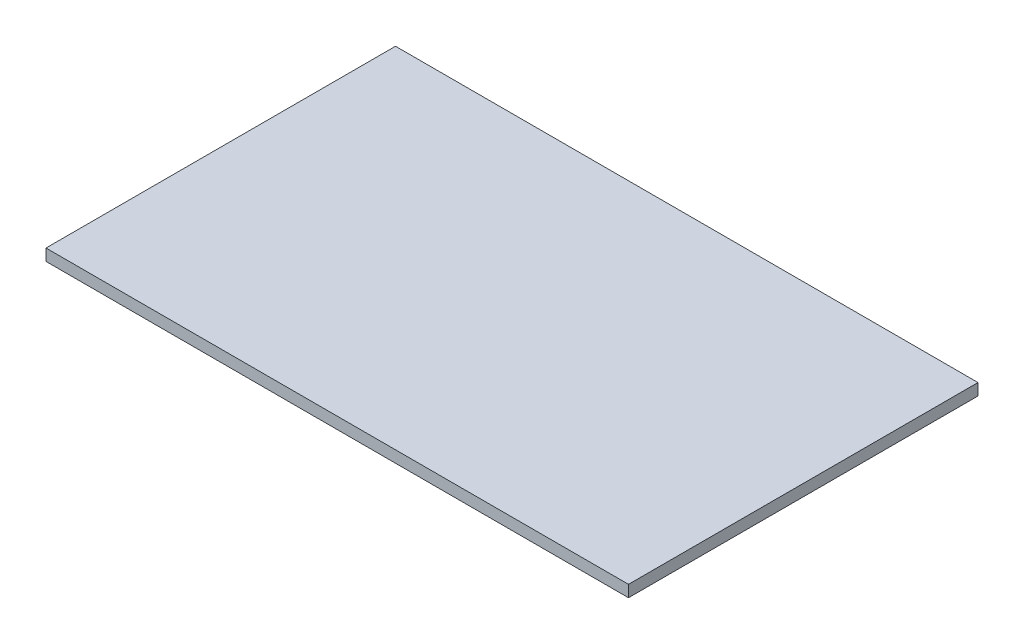
SolidWorks part; units mm, degrees
ref_plane "Front Plane" through (0, 0, 0) normal (0, 0, 1) x (1, 0, 0)
ref_plane "Top Plane" through (0, 0, 0) normal (0, 1, 0) x (1, 0, 0)
ref_plane "Right Plane" through (0, 0, 0) normal (1, 0, 0) x (0, 0, -1)
sketch "Sketch1" plane through (0, 0, 0) normal (0, 1, 0) x (1, 0, 0)
  line L1 (0, 0) -> (250, 0)
  line L2 (0, 0) -> (0, 150)
  line L3 (0, 150) -> (250, 150)
  line L4 (250, 0) -> (250, 150)
extrude "Boss-Extrude1" add sketch "Sketch1" along normal blind 5
